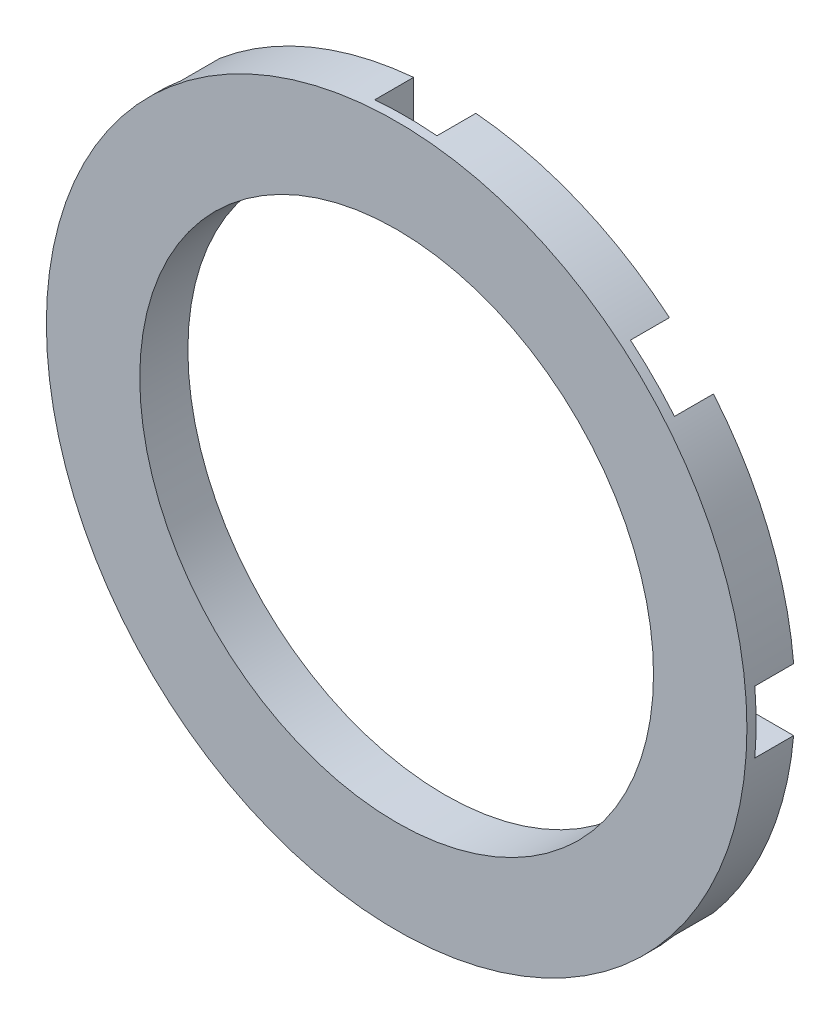
SolidWorks part; units mm, degrees
ref_plane "Front Plane" through (0, 0, 0) normal (0, 0, 1) x (1, 0, 0)
ref_plane "Top Plane" through (0, 0, 0) normal (0, 1, 0) x (1, 0, 0)
ref_plane "Right Plane" through (0, 0, 0) normal (1, 0, 0) x (0, 0, -1)
sketch "Sketch1" plane through (0, 0, 0) normal (0, 0, 1) x (1, 0, 0)
  circle A0 centre (0, 0) radius 28.575
  circle A1 centre (0, 0) radius 20.955
  dimension "D1" = 57.15
  dimension "D2" = 41.91
extrude "Boss-Extrude1" add sketch "Sketch1" along normal blind 1.9621 and the other way blind 1.9621
sketch "Sketch2" plane through (0, 0, 1.9621) normal (0, 0, 1) x (1, 0, 0)
  circle A0 centre (0, 0) radius 24.384
  circle A1 centre (0, 0) radius 23.114
  dimension "D1" = 46.228
  dimension "D2" = 48.768
extrude "Cut-Extrude1" [suppressed] cut sketch "Sketch2" against normal blind 0.8128 flip side to cut
mirror "Mirror1" [suppressed] about plane through (0, 0, 0) normal (0, 0, 1)
hole_wizard "#0-80 Tapped Hole1" positions "3DSketch2" profile "Sketch3" tap size "#0-80" standard "ANSI Inch"
sketch3d "3DSketch2"
  point P0 (0, 28.575, 0.0419)
sketch "Sketch3" plane through (0, 28.575, 0.0419) normal (1, 0, 0) x (0, 0, 1)
  line L0 (0, 0) -> (0, 3.6599)
  line L1 (0, 3.6599) -> (0.5956, 3.302)
  line L2 (0.5956, 3.302) -> (0.5956, 0)
  line L5 (0.5956, 0) -> (0, 0)
  line L10 (0, 3.6599) -> (-0.5956, 3.302) construction
  line L11 (0, -6.35) -> (0, 107.95) construction
  dimension "Tap Drill Dia." = 1.1913
  dimension "Tap Drill Depth" = 3.302
  dimension "Drill Angle" = 118
sketch "Sketch4" plane through (0, 0, -1.9621) normal (0, 0, -1) x (-1, 0, 0)
  circle A0 centre (0, 0) radius 25.4
  circle A1 centre (0, 0) radius 22.225
extrude "Cut-Extrude2" cut sketch "Sketch4" against normal blind 3.175
sketch "Sketch5" plane through (0, 0, -1.9621) normal (0, 0, -1) x (-1, 0, 0)
  line L0 (0, 31.115) -> (0, 24.765) construction
  line L1 (0, 25.4) -> (0, 28.575) construction
  line L2 (2.54, 31.115) -> (2.54, 24.765)
  line L3 (-2.54, 31.115) -> (-2.54, 24.765)
  arc A0 (2.54, 31.115) -> (-2.54, 31.115) centre (0, 31.115) ccw
  arc A1 (-2.54, 24.765) -> (2.54, 24.765) centre (0, 24.765) ccw
  point P4 (0, 27.94)
  dimension "D1" = 2.54
  dimension "D2" = 6.35
  dimension "D3" = 27.94
extrude "Cut-Extrude3" cut sketch "Sketch5" against normal up to surface (3.175 mm away) up to face at (-22.225, 0, 1.2129)
pattern_circular "CirPattern1" count 8 over 360 about axis through (0, 0, 0) along (0, 0, 1) of "Cut-Extrude3"
